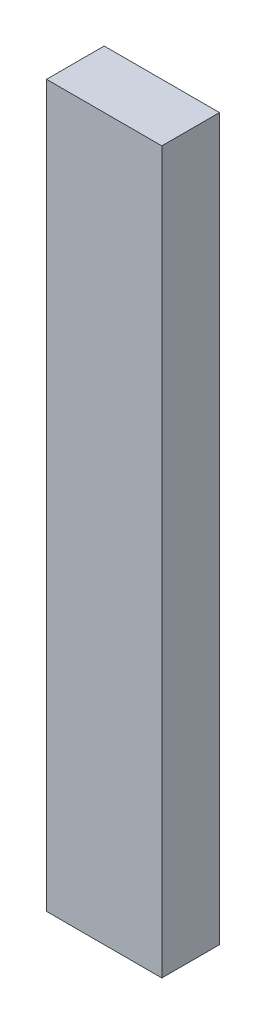
SolidWorks part; units mm, degrees
ref_plane "Front Plane" through (0, 0, 0) normal (0, 0, 1) x (1, 0, 0)
ref_plane "Top Plane" through (0, 0, 0) normal (0, 1, 0) x (1, 0, 0)
ref_plane "Right Plane" through (0, 0, 0) normal (1, 0, 0) x (0, 0, -1)
sketch "Sketch1" plane through (0, 0, 0) normal (0, 0, 1) x (1, 0, 0)
  line L1 (0, 0) -> (50.8, 0)
  line L2 (0, 0) -> (0, 317.5)
  line L3 (0, 317.5) -> (50.8, 317.5)
  line L4 (50.8, 0) -> (50.8, 317.5)
  dimension "D1" = 317.5
  dimension "D2" = 50.8
extrude "Boss-Extrude1" add sketch "Sketch1" along normal blind 25.4
